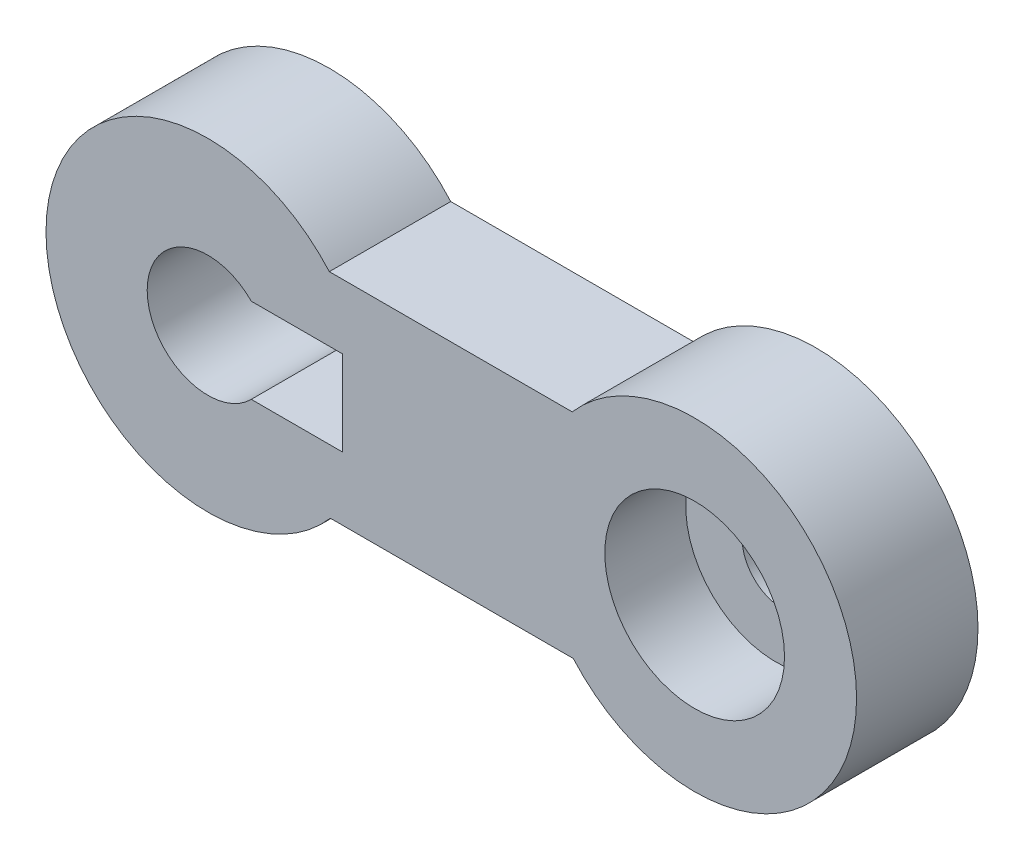
SolidWorks part; units mm, degrees
material "Plain Carbon Steel"
ref_plane "Front Plane" through (0, 0, 0) normal (0, 0, 1) x (1, 0, 0)
ref_plane "Top Plane" through (0, 0, 0) normal (0, 1, 0) x (1, 0, 0)
ref_plane "Right Plane" through (0, 0, 0) normal (1, 0, 0) x (0, 0, -1)
sketch "Sketch4" plane through (0, 0, 0) normal (0, 0, 1) x (1, 0, 0)
  line L1 (-31.834, -2.5642) -> (-1.834, -2.5642)
  line L3 (-31.9642, 23.7516) -> (-1.9642, 23.7516)
  arc A1 (-31.9642, 23.7516) -> (-31.834, -2.5642) centre (-46.961, 10.5192) ccw
  arc A2 (-1.834, -2.5642) -> (-1.9642, 23.7516) centre (13.1628, 10.6683) ccw
  point P0 (21.5548, 4.3109)
  dimension "D3" = 40
  dimension "D4" = 20
  dimension "D1" = 30
  dimension "D2" = 30
extrude "Boss-Extrude3" add sketch "Sketch4" along normal blind 15
sketch "Sketch5" plane through (0, 0, 15) normal (0, 0, 1) x (1, 0, 0)
  circle A1 centre (13.1628, 10.6683) radius 11.1
  arc A3 (-1.834, -2.5642) -> (-1.9642, 23.7516) centre (13.1628, 10.6683) ccw construction
  dimension "D4" = 22.2
  dimension "D2" = 0
extrude "Cut-Extrude2" cut sketch "Sketch5" against normal blind 10
sketch "Sketch8" plane through (0, 0, 5) normal (0, 0, 1) x (1, 0, 0)
  circle A0 centre (14.0306, 10.6683) radius 5
  circle A1 centre (13.1628, 10.6683) radius 11.1 construction
  dimension "D1" = 0
  dimension "D2" = 10
extrude "Cut-Extrude5" cut sketch "Sketch8" against normal blind 10
sketch "Sketch9" plane through (0, 0, 0) normal (0, 0, -1) x (-1, 0, 0)
  text T0 "G"
sketch "Sketch10" plane through (0, 0, 0) normal (0, 0, -1) x (-1, 0, 0)
  line L0 (42.3309, 5.2692) -> (42.3309, 15.7692)
  line L1 (42.3309, 5.2692) -> (30.3309, 5.2692)
  line L2 (42.3309, 15.7692) -> (30.3309, 15.7692)
  line L3 (30.3309, 5.2692) -> (30.3309, 15.7692)
  line L4 (31.834, -2.5642) -> (1.834, -2.5642) construction
  circle A0 centre (46.961, 10.5192) radius 7.5
  arc A1 (31.834, -2.5642) -> (31.9642, 23.7516) centre (46.961, 10.5192) ccw construction
  dimension "D1" = 0
  dimension "D2" = 15
  dimension "D3" = 7
  dimension "D4" = 7
  dimension "D5" = 12
  dimension "D6" = 10.5
  dimension "D7" = 180
extrude "Cut-Extrude6" cut sketch "Sketch10" against normal through all contours A0 L2 L3 L1 | L0 A0 | L0 A0
